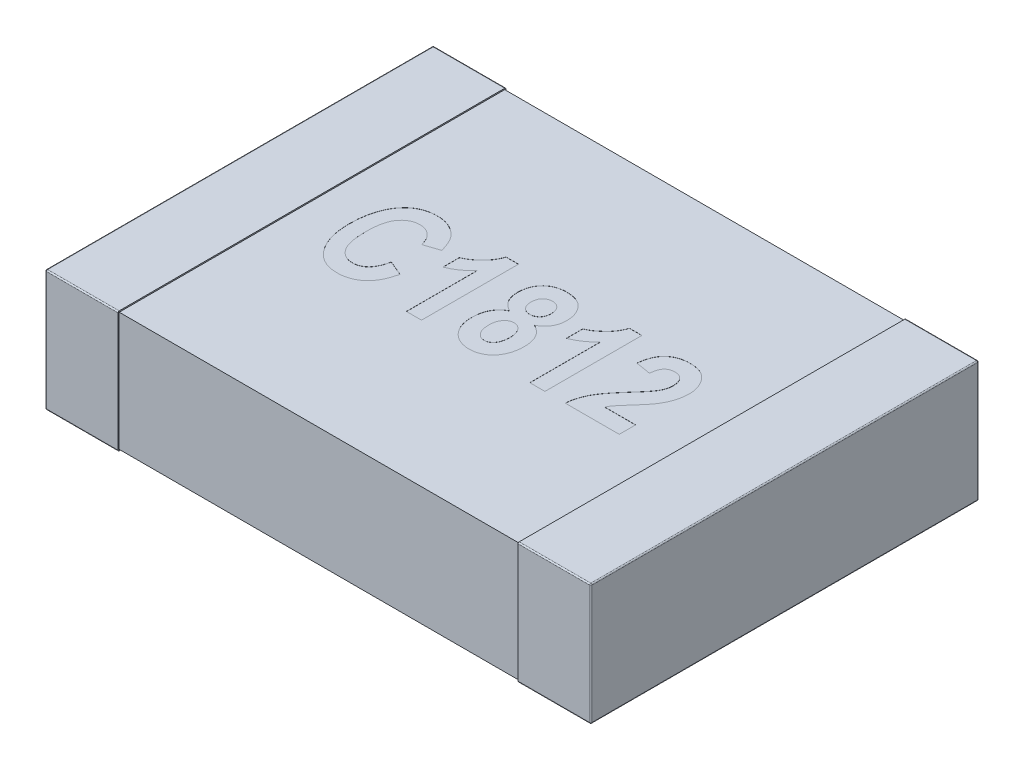
SolidWorks part; units mm, degrees
ref_plane "Front Plane" through (0, 0, 0) normal (0, 0, 1) x (1, 0, 0)
ref_plane "Top Plane" through (0, 0, 0) normal (0, 1, 0) x (1, 0, 0)
ref_plane "Right Plane" through (0, 0, 0) normal (1, 0, 0) x (0, 0, -1)
sketch "Sketch1" plane through (0, 0, 0) normal (0, 1, 0) x (1, 0, 0)
  line L0 (0, 0.15) -> (0, -0.15) construction
  line L1 (-2.25, 0) -> (0, 0) construction
  line L3 (-2.25, 1.6) -> (-1.65, 1.6)
  line L4 (-2.25, 1.6) -> (-2.25, -1.6)
  line L5 (-2.25, -1.6) -> (-1.65, -1.6)
  line L6 (-1.65, 1.6) -> (-1.65, -1.6)
  dimension "BANDWIDTH" = 0.6
  dimension "WIDTH" = 3.2
  dimension "LENGTH-HALF" = 2.25
extrude "THICKNESS" add sketch "Sketch1" along normal blind 1
fillet "Fillet1" radius 0.01 8 edges at (-2.25, 0, 0) (-1.95, 0, -1.6) (-2.25, 0.5, -1.6) (-1.95, 0, 1.6) (-2.25, 0.5, 1.6) (-2.25, 1, 0) (-1.95, 1, -1.6) (-1.95, 1, 1.6)
sketch "Sketch2" plane through (0, 0, 0) normal (1, 0, 0) x (0, 0, -1)
  line L0 (0, 1) -> (0, 0) construction
  line L1 (-1.59, 0.99) -> (1.59, 0.99)
  line L2 (-1.59, 0.99) -> (-1.59, 0.01)
  line L3 (-1.59, 0.01) -> (1.59, 0.01)
  line L4 (1.59, 0.99) -> (1.59, 0.01)
  line L5 (-1.59, 1) -> (1.59, 1) construction
  line L6 (-1.59, 0) -> (1.59, 0) construction
  line L7 (-1.6, 0.5) -> (1.6, 0.5) construction
  line L8 (-1.6, 0.99) -> (-1.6, 0.01) construction
  line L9 (1.6, 0.99) -> (1.6, 0.01) construction
  dimension "D1" = 0.01
  dimension "D2" = 0.01
extrude "Boss-Extrude2" add sketch "Sketch2" against normal up to surface (1.65 mm away) up to face at (-1.65, 0.5, 0)
mirror "Mirror3" about plane through (0, 0, 0) normal (1, 0, 0) of "Boss-Extrude2", "Fillet1", "THICKNESS"
sketch "Sketch3" plane through (0, 0.99, 0) normal (0, 1, 0) x (1, 0, 0)
  line L0 (-1.375, -0.4) -> (1.375, -0.4) construction
  line L1 (0, -0.55) -> (0, 0.55) construction
  line L2 (-0.55, 0) -> (0.55, 0) construction
  text T0 "<b>C1812</b>" font "Arial Narrow" height 0.8
  point P2 (0, -0.4)
  dimension "D1" = 2.75
  dimension "D2" = 0.4
extrude "Cut-Extrude1" cut sketch "Sketch3" against normal blind 0.001
